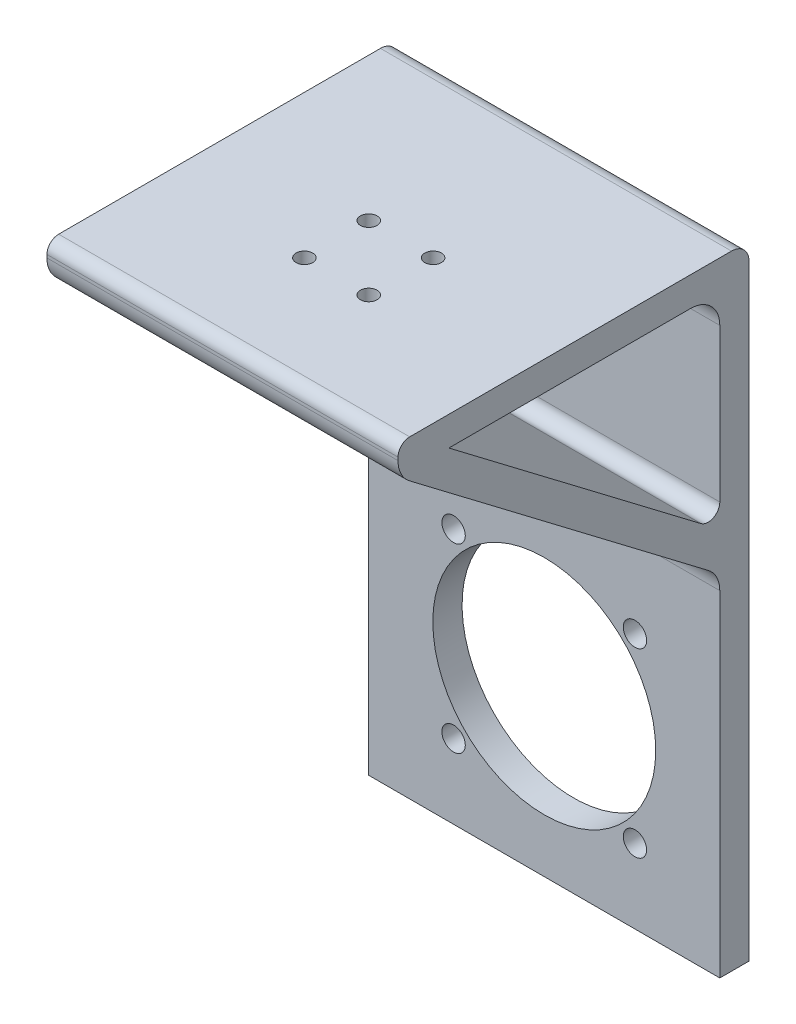
SolidWorks part; units mm, degrees
ref_plane "Front Plane" through (0, 0, 0) normal (0, 0, 1) x (1, 0, 0)
ref_plane "Top Plane" through (0, 0, 0) normal (0, 1, 0) x (1, 0, 0)
ref_plane "Right Plane" through (0, 0, 0) normal (1, 0, 0) x (0, 0, -1)
sketch "Sketch1" plane through (0, 0, 0) normal (1, 0, 0) x (0, 0, -1)
  line L2 (-20.4693, 47.095) -> (-20.4693, 52.095)
  line L3 (-20.4693, 52.095) -> (39.5307, 52.095)
  line L4 (39.5307, 52.095) -> (39.5307, -54.505)
  line L5 (39.5307, -54.505) -> (34.5307, -54.505)
  line L8 (34.5307, -54.505) -> (34.5307, 5.3146)
  line L9 (34.5307, 5.3146) -> (-20.4693, 47.095)
  line L10 (-11.7726, 47.095) -> (34.5307, 11.921)
  line L11 (34.5307, 11.921) -> (34.5307, 47.095)
  line L12 (34.5307, 47.095) -> (-11.7726, 47.095)
  dimension "D1" = 60
  dimension "D2" = 5
  dimension "D3" = 5
  dimension "D4" = 8.6967
  dimension "D5" = 106.6
  dimension "D6" = 35.174
  dimension "D7" = 90
extrude "Boss-Extrude1" add sketch "Sketch1" against normal blind 60
sketch "Sketch2" plane through (0, 52.095, 0) normal (0, 1, 0) x (1, 0, 0)
  line L0 (-30, 39.5307) -> (-30, -20.4693) construction
  line L3 (-60, 39.5307) -> (0, 39.5307) construction
  line L6 (-60, -20.4693) -> (0, -20.4693) construction
  line L13 (-60, 9.5307) -> (0, 9.5307) construction
  line L14 (-60, 39.5307) -> (-60, -20.4693) construction
  line L15 (0, 39.5307) -> (0, -20.4693) construction
  circle A4 centre (-35.5, 10.0307) radius 1.425
  circle A5 centre (-24.5, 10.0307) radius 1.425
  circle A6 centre (-24.5, -0.9693) radius 1.425
  circle A7 centre (-35.5, -0.9693) radius 1.425
  point P12 (-30, 4.5307)
  dimension "D4" = 2.85
  dimension "D5" = 2.85
  dimension "D6" = 2.85
  dimension "D7" = 2.85
  dimension "D1" = 35
  dimension "D2" = 11
  dimension "D3" = 11
extrude "Cut-Extrude2" cut sketch "Sketch2" against normal up to next
sketch "Sketch7" plane through (0, 0, -39.5307) normal (0, 0, -1) x (-1, 0, 0)
  line L0 (60, -54.505) -> (0, -54.505) construction
  circle A0 centre (14.5, -10.805) radius 2
  circle A1 centre (45.5, -10.805) radius 2
  circle A2 centre (45.5, -41.805) radius 2
  circle A3 centre (14.5, -41.805) radius 2
  circle A4 centre (30, -26.305) radius 19.05
  point P12 (30, -26.305)
  dimension "D6" = 4
  dimension "D7" = 4
  dimension "D8" = 4
  dimension "D9" = 4
  dimension "D10" = 38.1
  dimension "D1" = 31
  dimension "D2" = 31
  dimension "D3" = 12.7
  dimension "D4" = 28.2
  dimension "D11" = 21.9203
extrude "Cut-Extrude3" cut sketch "Sketch7" against normal up to next
fillet "Fillet2" radius 5 1 edges at (-30, 47.095, -34.5307)
fillet "Fillet4" radius 5 1 edges at (-30, 47.095, 20.4693)
fillet "Fillet5" radius 2 1 edges at (-30, 11.921, -34.5307)
fillet "Fillet6" radius 2 1 edges at (-30, 52.095, 20.4693)
fillet "Fillet7" radius 3 1 edges at (-30, 52.095, -39.5307)
fillet "Fillet8" radius 5 1 edges at (-30, 5.3146, -34.5307)
